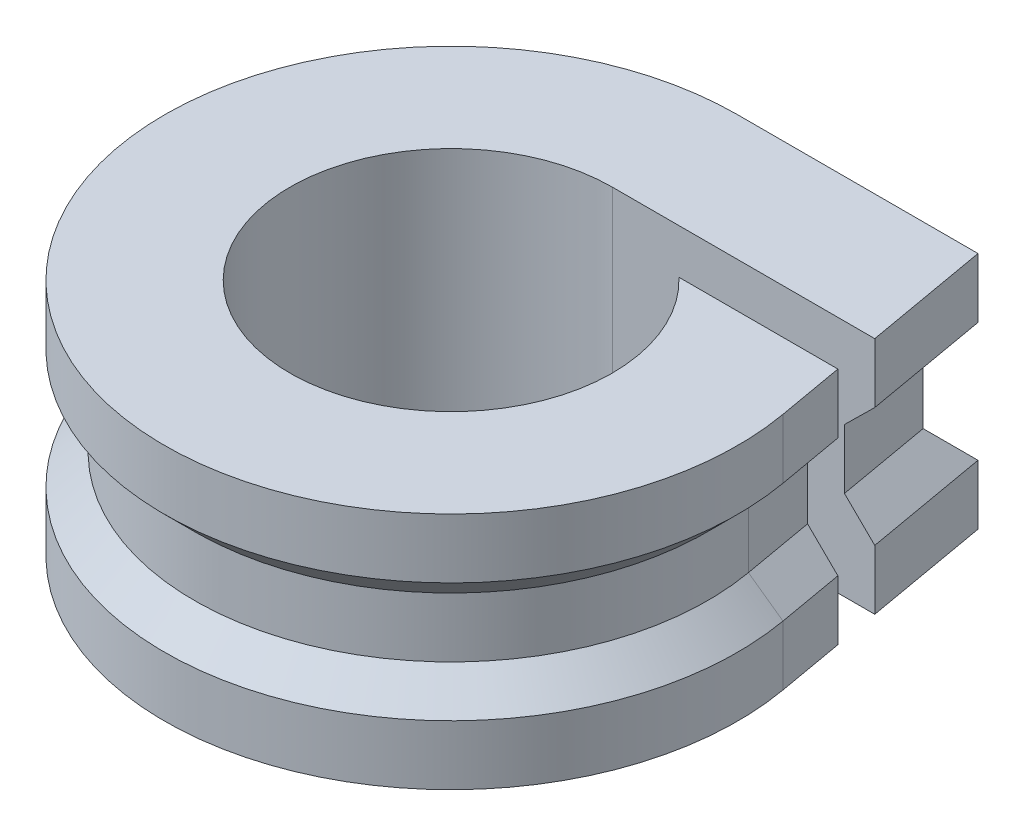
SolidWorks part; units mm, degrees
ref_plane "Front Plane" through (0, 0, 0) normal (0, 0, 1) x (1, 0, 0)
ref_plane "Top Plane" through (0, 0, 0) normal (0, 1, 0) x (1, 0, 0)
ref_plane "Right Plane" through (0, 0, 0) normal (1, 0, 0) x (0, 0, -1)
sketch "Sketch1" plane through (0, 0, 0) normal (0, 1, 0) x (1, 0, 0)
  line L0 (0, 9.6) -> (8.0554, 9.6)
  line L1 (8.0554, 9.6) -> (9.4542, 1.667)
  line L2 (0, 5.4) -> (8.7959, 5.4)
  line L3 (3.735, 3.9) -> (9.0604, 3.9)
  circle A0 centre (0, 0) radius 5.4
  arc A1 (0, 9.6) -> (9.4542, 1.667) centre (0, 0) ccw
  dimension "D1" = 10.8
  dimension "D2" = 4.2
  dimension "D3" = 100
  dimension "D4" = 1.5
extrude "Boss-Extrude1" add sketch "Sketch1" along normal blind 3 contours L0 A1 L1 L3 A0 L2
chamfer "Chamfer1" distance 1 angle 45 4 edges at (4.0277, 3, -9.6) (9.2573, 3, -2.7835) (-6.1708, 3, 7.354) (8.4256, 3, -7.5)
sketch "Sketch3" plane through (0, 3, 0) normal (0, 1, 0) x (1, 0, 0)
  line L9 (0, 5.4) -> (7.7805, 5.4)
  line L15 (7.7805, 5.4) -> (7.2163, 8.6)
  line L16 (7.2163, 8.6) -> (0, 8.6)
  line L19 (8.4693, 1.4934) -> (8.045, 3.9)
  line L20 (8.045, 3.9) -> (3.735, 3.9)
  line L21 (0, 5.4) -> (7.7805, 5.4)
  line L22 (7.7805, 5.4) -> (7.2163, 8.6)
  line L23 (7.2163, 8.6) -> (0, 8.6)
  line L24 (8.4693, 1.4934) -> (8.045, 3.9)
  line L25 (8.045, 3.9) -> (3.735, 3.9)
  arc A6 (0, 8.6) -> (8.4693, 1.4934) centre (0, 0) ccw
  arc A7 (0, 5.4) -> (3.735, 3.9) centre (0, 0) ccw
  arc A8 (0, 8.6) -> (8.4693, 1.4934) centre (0, 0) ccw
  arc A9 (0, 5.4) -> (3.735, 3.9) centre (0, 0) ccw
  dimension "D1" = 0
extrude "Boss-Extrude2" add sketch "Sketch3" along normal blind 1
mirror "Mirror1" about plane through (0, 4, 0) normal (0, 1, 0) of bodies 102
